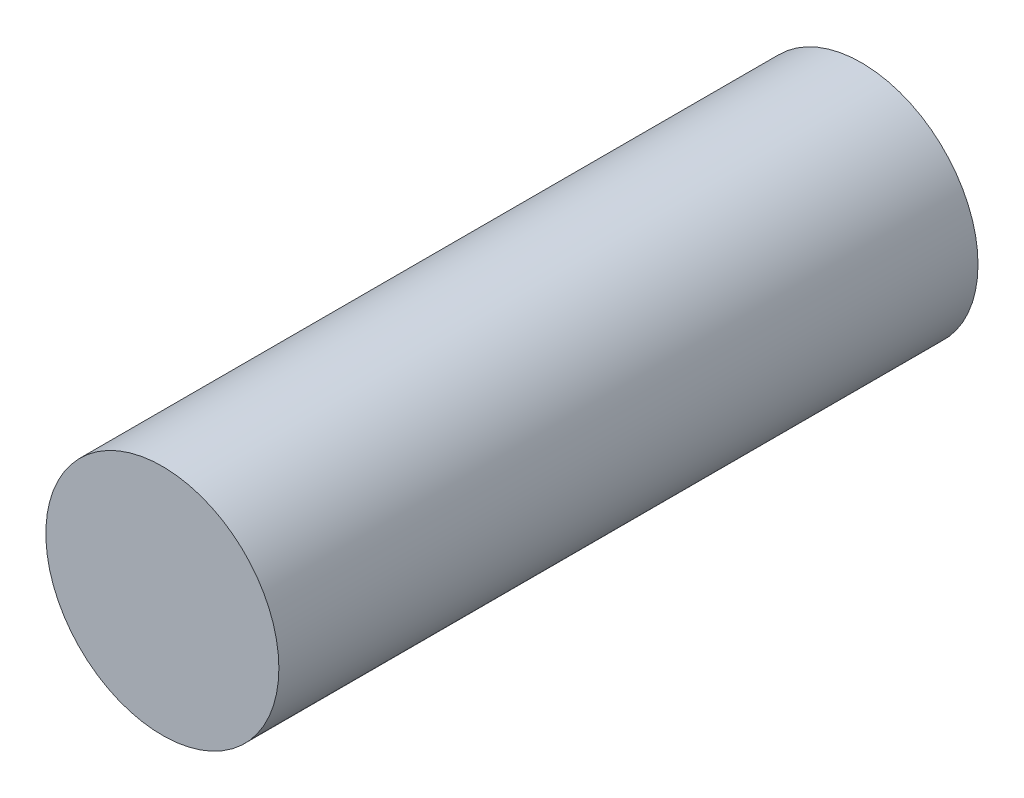
SolidWorks part; units mm, degrees
ref_plane "Front Plane" through (0, 0, 0) normal (0, 0, 1) x (1, 0, 0)
ref_plane "Top Plane" through (0, 0, 0) normal (0, 1, 0) x (1, 0, 0)
ref_plane "Right Plane" through (0, 0, 0) normal (1, 0, 0) x (0, 0, -1)
sketch "Sketch1" plane through (0, 0, 0) normal (0, 0, 1) x (1, 0, 0)
  circle A0 centre (0, 0) radius 2.5
  dimension "D1" = 5
extrude "Boss-Extrude1" add sketch "Sketch1" along normal blind 15
